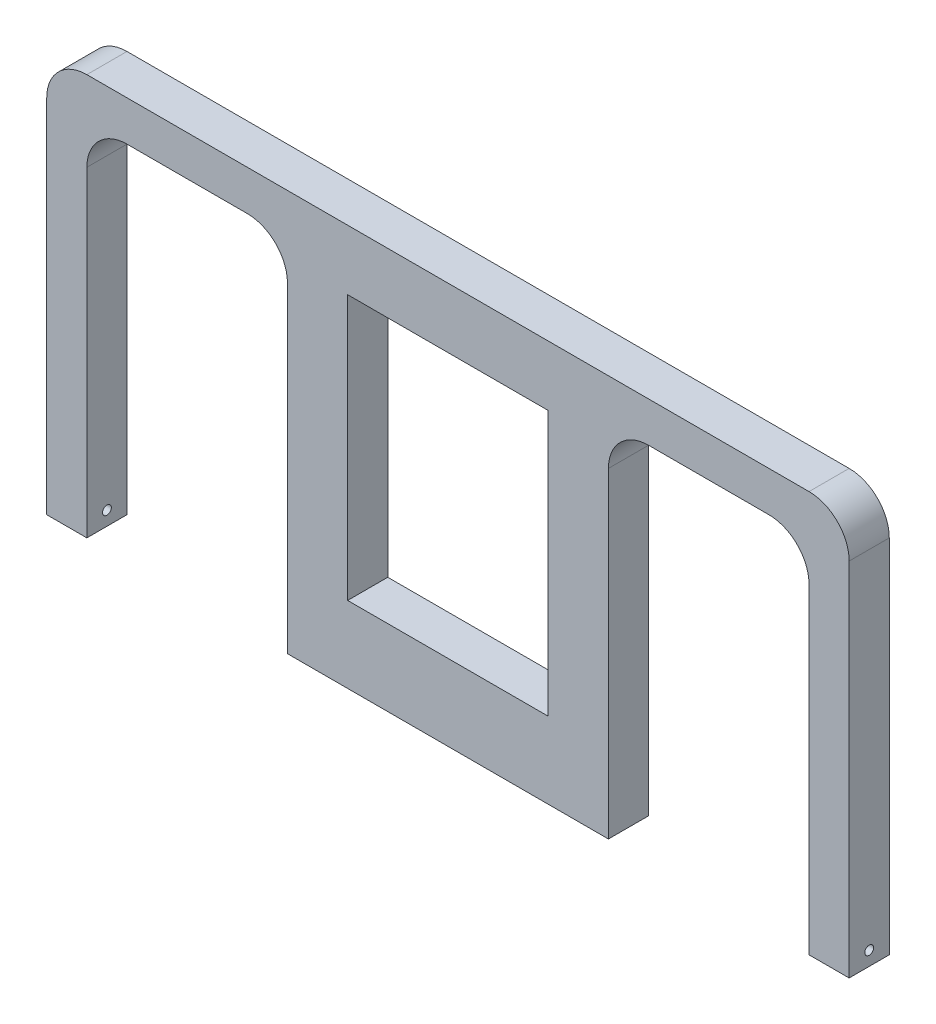
SolidWorks part; units mm, degrees
ref_plane "Front Plane" through (0, 0, 0) normal (0, 0, 1) x (1, 0, 0)
ref_plane "Top Plane" through (0, 0, 0) normal (0, 1, 0) x (1, 0, 0)
ref_plane "Right Plane" through (0, 0, 0) normal (1, 0, 0) x (0, 0, -1)
sketch "Sketch1" plane through (0, 0, 0) normal (0, 1, 0) x (1, 0, 0)
  line L0 (-114.3, 0) -> (114.3, 0) construction
  line L1 (-127, 0) -> (-114.3, 0)
  line L2 (-127, 0) -> (-127, -12.7)
  line L3 (-127, -12.7) -> (-114.3, -12.7)
  line L4 (-114.3, 0) -> (-114.3, -12.7)
  line L5 (127, -12.7) -> (114.3, -12.7)
  line L6 (127, -12.7) -> (127, 0)
  line L7 (127, 0) -> (114.3, 0)
  line L8 (114.3, -12.7) -> (114.3, 0)
  point P10 (0, 0)
  dimension "D1" = 12.7
  dimension "D2" = 228.6
extrude "Boss-Extrude1" add sketch "Sketch1" along normal blind 114.3
sketch "Sketch2" plane through (-127, 0, 0) normal (-1, 0, 0) x (0, 0, 1)
  line L0 (12.7, 114.3) -> (12.7, 0) construction
  line L1 (0, 114.3) -> (12.7, 114.3)
  line L2 (0, 114.3) -> (0, 127)
  line L3 (0, 127) -> (12.7, 127)
  line L4 (12.7, 114.3) -> (12.7, 127)
extrude "Boss-Extrude2" add sketch "Sketch2" against normal up to surface (254 mm away) up to face at (127, 57.15, 6.35)
sketch "Sketch3" plane through (0, 114.3, 0) normal (0, -1, 0) x (1, 0, 0)
  line L0 (-114.3, 6.35) -> (114.3, 6.35) construction
  line L1 (-114.3, 12.7) -> (-114.3, 0) construction
  line L2 (114.3, 0) -> (114.3, 12.7) construction
  line L3 (114.3, 0) -> (-114.3, 0) construction
  line L4 (50.8, 12.7) -> (-50.8, 12.7)
  line L5 (50.8, 12.7) -> (50.8, 0)
  line L6 (50.8, 0) -> (-50.8, 0)
  line L7 (-50.8, 12.7) -> (-50.8, 0)
  line L8 (50.8, 12.7) -> (-50.8, 0) construction
  line L9 (50.8, 0) -> (-50.8, 12.7) construction
  point P6 (0, 6.35)
  dimension "D1" = 101.6
extrude "Boss-Extrude3" add sketch "Sketch3" along normal blind 114.3
sketch "Sketch4" plane through (127, 0, 0) normal (1, 0, 0) x (0, 0, -1)
  line L0 (-12.7, 4.445) -> (0, 4.445) construction
  line L1 (-12.7, 0) -> (-12.7, 127) construction
  line L2 (0, 127) -> (0, 0) construction
  line L3 (-12.7, 0) -> (0, 0) construction
  circle A0 centre (-6.35, 4.445) radius 1.397
  point P9 (-6.35, 4.445)
  dimension "D1" = 2.794
  dimension "D2" = 4.445
extrude "Cut-Extrude1" cut sketch "Sketch4" against normal up to next (12.7 mm away)
mirror "Mirror1" about plane through (0, 0, 0) normal (1, 0, 0) of "Cut-Extrude1"
sketch "Sketch5" plane through (0, 0, 0) normal (0, 0, -1) x (-1, 0, 0)
  line L0 (-114.3, 114.3) -> (-114.3, 101.6)
  line L1 (-114.3, 114.3) -> (-114.3, 0) construction
  line L2 (-114.3, 114.3) -> (-101.6, 114.3)
  line L3 (-114.3, 114.3) -> (-50.8, 114.3) construction
  line L4 (-50.8, 114.3) -> (-63.5, 114.3)
  line L5 (-50.8, 114.3) -> (-50.8, 101.6)
  line L6 (-50.8, 0) -> (-50.8, 114.3) construction
  arc A0 (-114.3, 101.6) -> (-101.6, 114.3) centre (-101.6, 101.6) cw
  arc A1 (-50.8, 101.6) -> (-63.5, 114.3) centre (-63.5, 101.6) ccw
  dimension "D1" = 12.7
extrude "Boss-Extrude4" add sketch "Sketch5" against normal blind 12.7
mirror "Mirror2" about plane through (0, 0, 0) normal (1, 0, 0) of "Boss-Extrude4"
sketch "Sketch6" plane through (0, 0, 0) normal (0, 0, -1) x (-1, 0, 0)
  line L0 (-127, 127) -> (-127, 114.3)
  line L1 (-127, 127) -> (-127, 0) construction
  line L2 (-127, 127) -> (-114.3, 127)
  line L3 (-127, 127) -> (127, 127) construction
  arc A0 (-127, 114.3) -> (-114.3, 127) centre (-114.3, 114.3) cw
  dimension "D1" = 12.7
extrude "Cut-Extrude2" cut sketch "Sketch6" against normal blind 12.7
mirror "Mirror3" about plane through (0, 0, 0) normal (1, 0, 0) of "Cut-Extrude2"
sketch "Sketch7" plane through (0, 0, 0) normal (0, 0, -1) x (-1, 0, 0)
  line L0 (-114.3, 127) -> (114.3, 127) construction
  line L1 (-31.75, 107.95) -> (31.75, 107.95)
  line L2 (-31.75, 107.95) -> (-31.75, 24.13)
  line L3 (-31.75, 24.13) -> (31.75, 24.13)
  line L4 (31.75, 107.95) -> (31.75, 24.13)
  line L5 (-31.75, 107.95) -> (31.75, 24.13) construction
  line L6 (-31.75, 24.13) -> (31.75, 107.95) construction
  line L7 (-50.8, 0) -> (-50.8, 101.6) construction
  line L8 (50.8, 0) -> (50.8, 101.6) construction
  line L9 (50.8, 0) -> (-50.8, 0) construction
  point P0 (0, 66.04)
  dimension "D1" = 19.05
  dimension "D2" = 19.05
  dimension "D3" = 19.05
  dimension "D4" = 24.13
extrude "Cut-Extrude3" cut sketch "Sketch7" against normal blind 12.7
